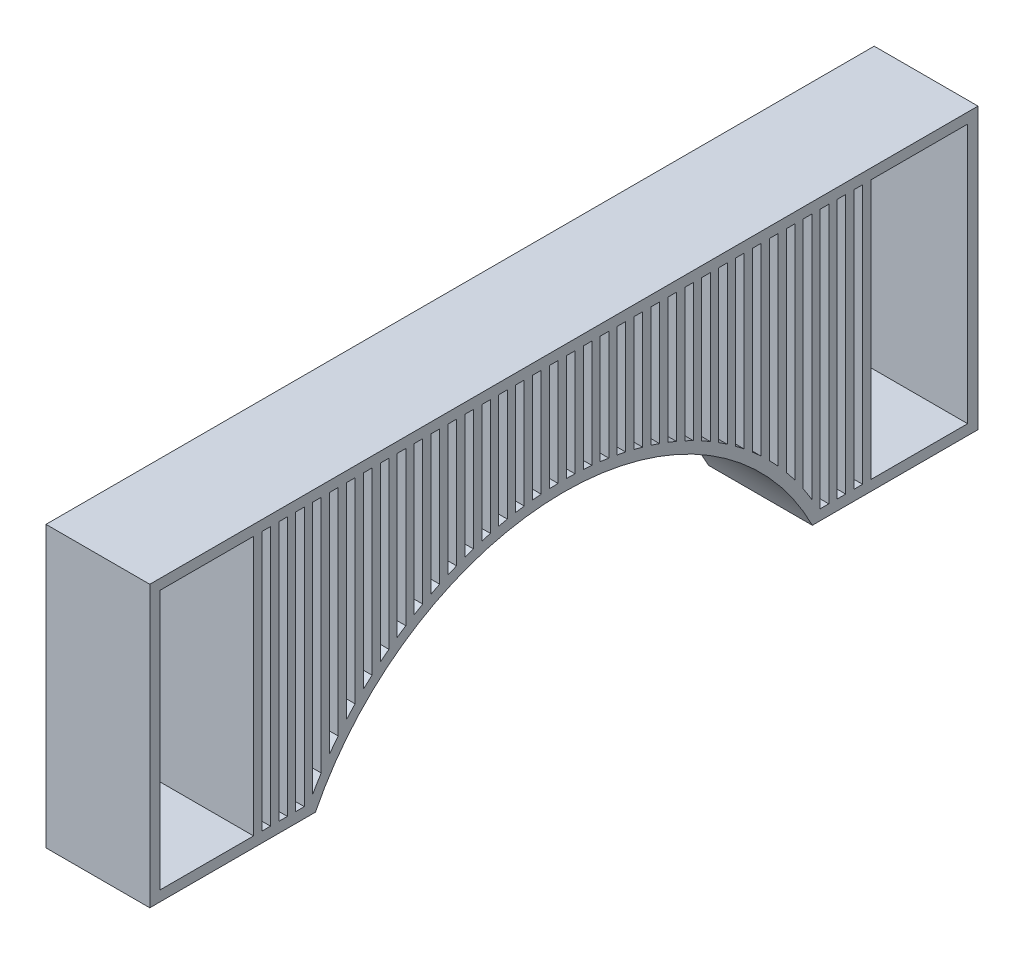
SolidWorks part; units mm, degrees
material "6061 Alloy"
ref_plane "Front Plane" through (0, 0, 0) normal (0, 0, 1) x (1, 0, 0)
ref_plane "Top Plane" through (0, 0, 0) normal (0, 1, 0) x (1, 0, 0)
ref_plane "Right Plane" through (0, 0, 0) normal (1, 0, 0) x (0, 0, -1)
sketch "Sketch1" plane through (0, 0, 0) normal (1, 0, 0) x (0, 0, -1)
  line L0 (18.792, 0) -> (29.9, 0)
  line L1 (-18.792, 0) -> (-29.9, 0)
  line L2 (-21.8, -11.05) -> (21.8, -11.05)
  line L3 (-29.9, 0) -> (-29.9, -11.05)
  line L4 (-29.9, -11.05) -> (-21.8, -11.05)
  line L5 (21.8, -11.05) -> (29.9, -11.05)
  line L6 (29.9, -11.05) -> (29.9, 0)
  line L7 (-29.9, 0) -> (-29.9, 1)
  line L8 (-29.9, 1) -> (-23.9382, 1)
  line L9 (23.9382, 1) -> (29.9, 1)
  line L10 (-24.5466, 2) -> (-39.9, 2)
  line L163 (-39.9, 2) -> (-39.9, 1)
  line L164 (-39.9, 1) -> (-23.9382, 1)
  line L165 (24.5466, 2) -> (39.9, 2)
  line L166 (29.9, 1) -> (29.9, 0)
  line L167 (39.9, 2) -> (39.9, 1)
  line L168 (39.9, 1) -> (23.9382, 1)
  line L169 (-28.27, 2) -> (-28.27, 27)
  line L174 (-29.9, 2) -> (-29.1, 2)
  line L175 (-29.9, 2) -> (-29.9, 27)
  line L176 (-29.9, 27) -> (-29.1, 27)
  line L177 (-29.1, 2) -> (-29.1, 27)
  line L178 (-28.27, 2) -> (-27.47, 2)
  line L179 (-27.47, 2) -> (-27.47, 27)
  line L180 (-28.27, 27) -> (-27.47, 27)
  line L181 (-26.64, 2) -> (-26.64, 27)
  line L182 (-26.64, 2) -> (-25.84, 2)
  line L183 (-39.9, 2) -> (-39.9, 28)
  line L184 (-39.9, 28) -> (39.9, 28)
  line L185 (-25.84, 2) -> (-25.84, 27)
  line L186 (39.9, 28) -> (39.9, 2)
  line L187 (-38.9, 2) -> (-38.9, 27)
  line L188 (-26.64, 27) -> (-25.84, 27)
  line L189 (-38.9, 27) -> (38.9, 27)
  line L190 (38.9, 27) -> (38.9, 2)
  line L191 (-25.01, 2) -> (-25.01, 27)
  line L192 (-25.01, 2) -> (-24.5466, 2)
  line L193 (-24.21, 2.6144) -> (-24.21, 27)
  line L194 (-25.01, 27) -> (-24.21, 27)
  line L195 (-23.38, 2) -> (-23.38, 2.0502)
  line L198 (-23.38, 27) -> (-22.58, 27)
  line L202 (-21.75, 27) -> (-20.95, 27)
  line L206 (-20.12, 27) -> (-19.32, 27)
  line L210 (-18.49, 27) -> (-17.69, 27)
  line L214 (-16.86, 27) -> (-16.06, 27)
  line L218 (-15.23, 27) -> (-14.43, 27)
  line L222 (-13.6, 27) -> (-12.8, 27)
  line L226 (-11.97, 27) -> (-11.17, 27)
  line L230 (-10.34, 27) -> (-9.54, 27)
  line L234 (-8.71, 27) -> (-7.91, 27)
  line L238 (-7.08, 27) -> (-6.28, 27)
  line L242 (-5.45, 27) -> (-4.65, 27)
  line L246 (-3.82, 27) -> (-3.02, 27)
  line L250 (-2.19, 27) -> (-1.39, 27)
  line L254 (-0.56, 27) -> (0.24, 27)
  line L258 (1.07, 27) -> (1.87, 27)
  line L262 (2.7, 27) -> (3.5, 27)
  line L266 (4.33, 27) -> (5.13, 27)
  line L270 (5.96, 27) -> (6.76, 27)
  line L274 (7.59, 27) -> (8.39, 27)
  line L278 (9.22, 27) -> (10.02, 27)
  line L282 (10.85, 27) -> (11.65, 27)
  line L286 (12.48, 27) -> (13.28, 27)
  line L290 (14.11, 27) -> (14.91, 27)
  line L294 (15.74, 27) -> (16.54, 27)
  line L298 (17.37, 27) -> (18.17, 27)
  line L302 (19, 27) -> (19.8, 27)
  line L306 (20.63, 27) -> (21.43, 27)
  line L310 (22.26, 27) -> (23.06, 27)
  line L311 (23.89, 3.1665) -> (23.89, 27)
  line L312 (24.5466, 2) -> (24.69, 2)
  line L313 (24.69, 2) -> (24.69, 27)
  line L314 (23.89, 27) -> (24.69, 27)
  line L315 (25.52, 2) -> (25.52, 27)
  line L316 (25.52, 2) -> (26.32, 2)
  line L317 (26.32, 2) -> (26.32, 27)
  line L318 (25.52, 27) -> (26.32, 27)
  line L319 (27.15, 2) -> (27.15, 27)
  line L320 (27.15, 2) -> (27.95, 2)
  line L321 (27.95, 2) -> (27.95, 27)
  line L322 (27.15, 27) -> (27.95, 27)
  line L323 (28.78, 2) -> (28.78, 27)
  line L324 (28.78, 2) -> (29.58, 2)
  line L325 (29.58, 2) -> (29.58, 27)
  line L326 (28.78, 27) -> (29.58, 27)
  line L327 (-23.38, 3.9905) -> (-23.38, 27)
  line L328 (-22.58, 5.1668) -> (-22.58, 27)
  line L329 (-21.75, 6.2641) -> (-21.75, 27)
  line L330 (-20.95, 7.224) -> (-20.95, 27)
  line L331 (-20.12, 8.134) -> (-20.12, 27)
  line L332 (-19.32, 8.9394) -> (-19.32, 27)
  line L333 (-18.49, 9.7096) -> (-18.49, 27)
  line L334 (-17.69, 10.3954) -> (-17.69, 27)
  line L335 (-16.86, 11.0539) -> (-16.86, 27)
  line L336 (-16.06, 11.6418) -> (-16.06, 27)
  line L337 (-15.23, 12.207) -> (-15.23, 27)
  line L338 (-14.43, 12.7116) -> (-14.43, 27)
  line L507 (23.06, 4.4766) -> (23.06, 27)
  line L508 (22.26, 5.6033) -> (22.26, 27)
  line L512 (21.43, 6.6586) -> (21.43, 27)
  line L513 (20.63, 7.5845) -> (20.63, 27)
  line L517 (-13.6, 13.1962) -> (-13.6, 27)
  line L518 (-12.8, 13.6279) -> (-12.8, 27)
  line L519 (-11.97, 14.041) -> (-11.97, 27)
  line L520 (-11.17, 14.4072) -> (-11.17, 27)
  line L521 (-10.34, 14.7555) -> (-10.34, 27)
  line L522 (-9.54, 15.0618) -> (-9.54, 27)
  line L523 (-8.71, 15.3503) -> (-8.71, 27)
  line L524 (-7.91, 15.6009) -> (-7.91, 27)
  line L525 (-7.08, 15.8333) -> (-7.08, 27)
  line L526 (-6.28, 16.0314) -> (-6.28, 27)
  line L527 (-5.45, 16.2105) -> (-5.45, 27)
  line L528 (-4.65, 16.3583) -> (-4.65, 27)
  line L529 (-3.82, 16.4863) -> (-3.82, 27)
  line L530 (-3.02, 16.5855) -> (-3.02, 27)
  line L531 (-2.19, 16.6636) -> (-2.19, 27)
  line L532 (-1.39, 16.7152) -> (-1.39, 27)
  line L533 (-0.56, 16.7444) -> (-0.56, 27)
  line L534 (0.24, 16.749) -> (0.24, 27)
  line L535 (1.07, 16.7294) -> (1.07, 27)
  line L536 (1.87, 16.687) -> (1.87, 27)
  line L537 (2.7, 16.6186) -> (2.7, 27)
  line L538 (3.5, 16.5288) -> (3.5, 27)
  line L539 (4.33, 16.4107) -> (4.33, 27)
  line L540 (5.13, 16.2726) -> (5.13, 27)
  line L541 (5.96, 16.1036) -> (5.96, 27)
  line L542 (6.76, 15.9156) -> (6.76, 27)
  line L543 (7.59, 15.6938) -> (7.59, 27)
  line L544 (8.39, 15.4537) -> (8.39, 27)
  line L545 (9.22, 15.1765) -> (9.22, 27)
  line L546 (10.02, 14.8814) -> (10.02, 27)
  line L547 (10.85, 14.5453) -> (10.85, 27)
  line L548 (11.65, 14.1912) -> (11.65, 27)
  line L549 (12.48, 13.7913) -> (12.48, 27)
  line L550 (13.28, 13.373) -> (13.28, 27)
  line L551 (14.11, 12.903) -> (14.11, 27)
  line L552 (14.91, 12.4134) -> (14.91, 27)
  line L553 (15.74, 11.8649) -> (15.74, 27)
  line L554 (16.54, 11.2943) -> (16.54, 27)
  line L555 (17.37, 10.6554) -> (17.37, 27)
  line L556 (18.17, 9.9902) -> (18.17, 27)
  line L557 (19, 9.2438) -> (19, 27)
  line L558 (19.8, 8.4641) -> (19.8, 27)
  arc A0 (21.8, -11.05) -> (-21.8, -11.05) centre (0, -11.05) ccw
  arc A3 (23.9382, 1) -> (-23.9382, 1) centre (0, -11.05) ccw
  arc A4 (23.3139, 0) -> (-23.3139, 0) centre (0, -11.05) ccw
  arc A5 (24.5466, 2) -> (-24.5466, 2) centre (0, -11.05) ccw
  point P47 (34.4187, -11.05)
  dimension "D1" = 21.8
  dimension "D5" = 0.8
  dimension "D10" = 1
  dimension "D11" = 1
  dimension "D2" = 11.05
  dimension "D3" = 8.1
  dimension "D4" = 8.1
  dimension "D6" = 1
  dimension "D8" = 1
  dimension "D12" = 10
  dimension "D9" = 1
  dimension "D13" = 10
  dimension "D16" = 1
  dimension "D17" = 1
  dimension "D18" = 1
extrude "Boss-Extrude1" add sketch "Sketch1" along normal blind 10 contours L189 | L10 L177 L176 L175 | L180 L169 L10 L179 | L188 L181 L10 L185 | A5 L193 L189 L191 L10 | A5 L328 L189 L327 | A5 L330 L189 L329 | A5 L332 L189 L331 | A5 L334 L189 L333 | A5 L336 L189 L335 | A5 L338 L189 L337 | A5 L518 L189 L517 | A5 L520 L189 L519 | A5 L522 L189 L521 | A5 L524 L189 L523 | A5 L526 L189 L525 | A5 L528 L189 L527 | A5 L530 L189 L529 | A5 L532 L189 L531 | A5 L534 L189 L533 | A5 L536 L189 L535 | A5 L538 L189 L537 | A5 L540 L189 L539 | A5 L542 L189 L541 | A5 L544 L189 L543 | A5 L546 L189 L545 | A5 L548 L189 L547 | A5 L550 L189 L549 | A5 L552 L189 L551 | A5 L554 L189 L553 | A5 L556 L189 L555 | A5 L558 L189 L557 | A5 L512 L189 L513 | A5 L507 L189 L508 | A5 L165 L313 L189 L311 | L165 L317 L189 L315 | L165 L321 L189 L319 | L165 L325 L189 L323 | L165 A5
